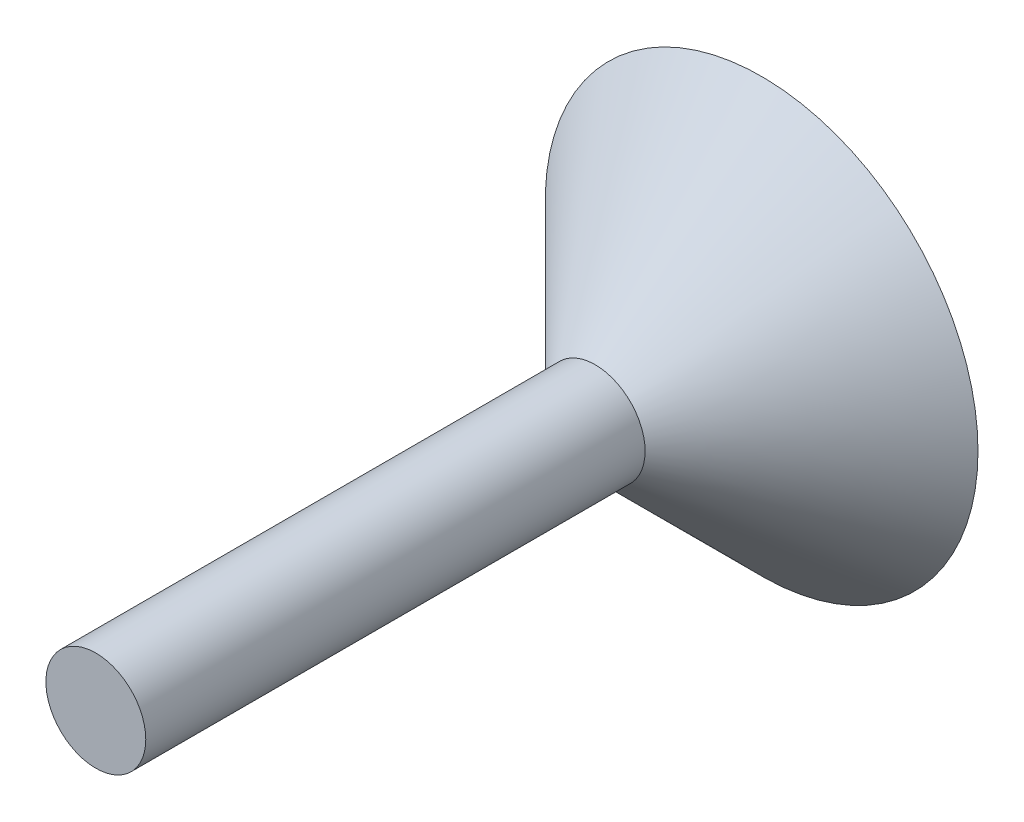
SolidWorks part; units mm, degrees
ref_plane "Front Plane" through (0, 0, 0) normal (0, 0, 1) x (1, 0, 0)
ref_plane "Top Plane" through (0, 0, 0) normal (0, 1, 0) x (1, 0, 0)
ref_plane "Right Plane" through (0, 0, 0) normal (1, 0, 0) x (0, 0, -1)
sketch "Sketch1" plane through (0, 0, 0) normal (1, 0, 0) x (0, 0, -1)
  line L0 (0, 0) -> (114.3746, 0) construction
  line L1 (0, 0) -> (0, -3)
  line L2 (0, -3) -> (30, -3)
  line L3 (30, -3) -> (40, -13)
  line L4 (40, -13) -> (40, 0)
  line L5 (0, 0) -> (40, 0)
  point P7 (40, -14.5666)
  point P8 (40, 0)
  dimension "D1" = 3
  dimension "D2" = 45
  dimension "D3" = 40
  dimension "D4" = 10
revolve "Revolve1" add sketch "Sketch1" angle 360 about L0
